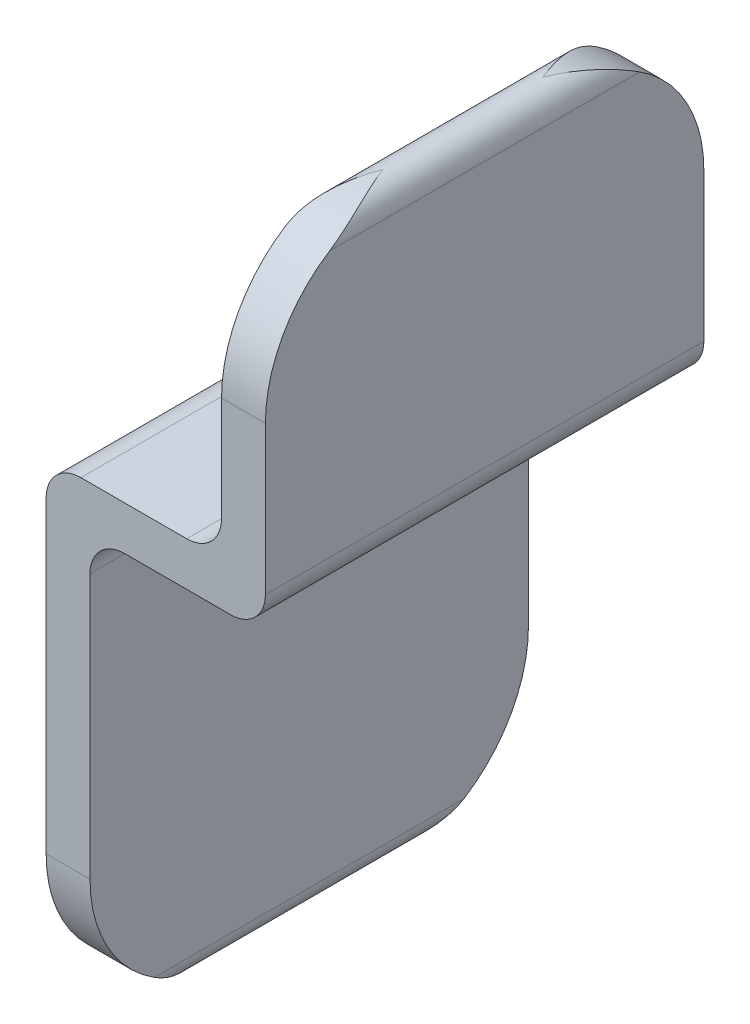
SolidWorks part; units mm, degrees
ref_plane "Front Plane" through (0, 0, 0) normal (0, 0, 1) x (1, 0, 0)
ref_plane "Top Plane" through (0, 0, 0) normal (0, 1, 0) x (1, 0, 0)
ref_plane "Right Plane" through (0, 0, 0) normal (1, 0, 0) x (0, 0, -1)
sketch "Sketch1" plane through (0, 0, 0) normal (0, 0, 1) x (1, 0, 0)
  line L0 (0, 0) -> (0, -12.7)
  line L1 (0, -12.7) -> (-8, -12.7)
  line L2 (-8, -12.7) -> (-8, -32.7)
  line L3 (-1, 0) -> (-1, -10.1125)
  line L4 (-2.5875, -11.7) -> (-7.4125, -11.7)
  line L5 (-9, -13.2875) -> (-9, -32.7)
  line L6 (1, 0) -> (1, -12.1125)
  line L7 (-0.5875, -13.7) -> (-5.4125, -13.7)
  line L8 (-7, -15.2875) -> (-7, -32.7)
  line L9 (1, -13.7) -> (-7, -13.7) construction
  line L10 (-7, -13.7) -> (-7, -32.7) construction
  line L11 (-1, 0) -> (-1, -11.7) construction
  line L12 (-1, -11.7) -> (-9, -11.7) construction
  line L13 (1, 0) -> (1, -13.7) construction
  line L14 (-9, -11.7) -> (-9, -32.7) construction
  arc A0 (-1, 0) -> (1, 0) centre (0, 0) cw
  arc A1 (-9, -32.7) -> (-7, -32.7) centre (-8, -32.7) ccw
  arc A2 (-5.4125, -13.7) -> (-7, -15.2875) centre (-5.4125, -15.2875) ccw
  arc A3 (-1, -10.1125) -> (-2.5875, -11.7) centre (-2.5875, -10.1125) cw
  arc A4 (1, -12.1125) -> (-0.5875, -13.7) centre (-0.5875, -12.1125) cw
  arc A5 (-9, -13.2875) -> (-7.4125, -11.7) centre (-7.4125, -13.2875) cw
  dimension "D6" = 1.5875
  dimension "D7" = 1.5875
  dimension "D8" = 1.5875
  dimension "D9" = 1.5875
  dimension "D1" = 12.7
  dimension "D2" = 8
  dimension "D3" = 20
  dimension "D4" = 1
  dimension "D5" = 1
extrude "Boss-Extrude1" add sketch "Sketch1" along normal blind 20
sketch "Sketch2" plane through (-9, 0, 0) normal (-1, 0, 0) x (0, 0, 1)
  line L1 (6.35, 1) -> (13.65, 1)
  line L2 (0, -5.35) -> (0, -27.35)
  line L3 (6.35, -33.7) -> (13.65, -33.7)
  line L4 (20, -5.35) -> (20, -27.35)
  line L5 (0, -33.7) -> (20, -33.7)
  line L6 (0, -33.7) -> (0, 1)
  line L7 (0, 1) -> (20, 1)
  line L8 (20, -33.7) -> (20, 1)
  arc A0 (6.35, -33.7) -> (0, -27.35) centre (6.35, -27.35) cw
  arc A1 (13.65, -33.7) -> (20, -27.35) centre (13.65, -27.35) ccw
  arc A2 (20, -5.35) -> (13.65, 1) centre (13.65, -5.35) ccw
  arc A3 (0, -5.35) -> (6.35, 1) centre (6.35, -5.35) cw
  point P10 (20, -33.7)
  point P15 (0, 1)
  line M9 (0, -13.2875) -> (0, -32.7)
  line M10 (0, -32.7) -> (20, -32.7)
  line M11 (20, -32.7) -> (20, -13.2875)
  dimension "D1" = 6.35
  dimension "D2" = 6.35
  dimension "D3" = 6.35
  dimension "D4" = 6.35
extrude "Cut-Extrude1" cut sketch "Sketch2" against normal blind 55 contours L6 A3 L7 | A2 L8 L7 | A1 M10 M11 | A1 L5 L8 M10 | A0 M10 M9 | L5 A0 L6 M10
equation "\"Bracket Width\" = 20mm"
equation "\"Sheet Thickness\" = 2mm"
equation "\"Top Portion Height\" = 0.5in"
equation "\"Top Overhang\" = 8mm"
equation "\"Bracket Body Height\" = 20mm"
equation "\"Bracket Edge Fillet\" = 0.25in"
equation "\"Bend Fillet\" = 0.125in"
equation "\"D1@Sketch1\"=\"Top Portion Height\""
equation "\"D2@Sketch1\"=\"Top Overhang\""
equation "\"D3@Sketch1\"=\"Bracket Body Height\""
equation "\"D4@Sketch1\"=\"Sheet Thickness\"/2"
equation "\"D9@Sketch1\"=\"Bend Fillet\"/2"
equation "\"D6@Sketch1\"=\"Bend Fillet\"/2"
equation "\"D7@Sketch1\"=\"Bend Fillet\"/2"
equation "\"D8@Sketch1\"=\"Bend Fillet\"/2"
equation "\"D1@Boss-Extrude1\"=\"Bracket Width\""
equation "\"D3@Sketch2\"=\"Bracket Edge Fillet\""
equation "\"D4@Sketch2\"=\"Bracket Edge Fillet\""
equation "\"D1@Sketch2\"=\"Bracket Edge Fillet\""
equation "\"D2@Sketch2\"=\"Bracket Edge Fillet\""
